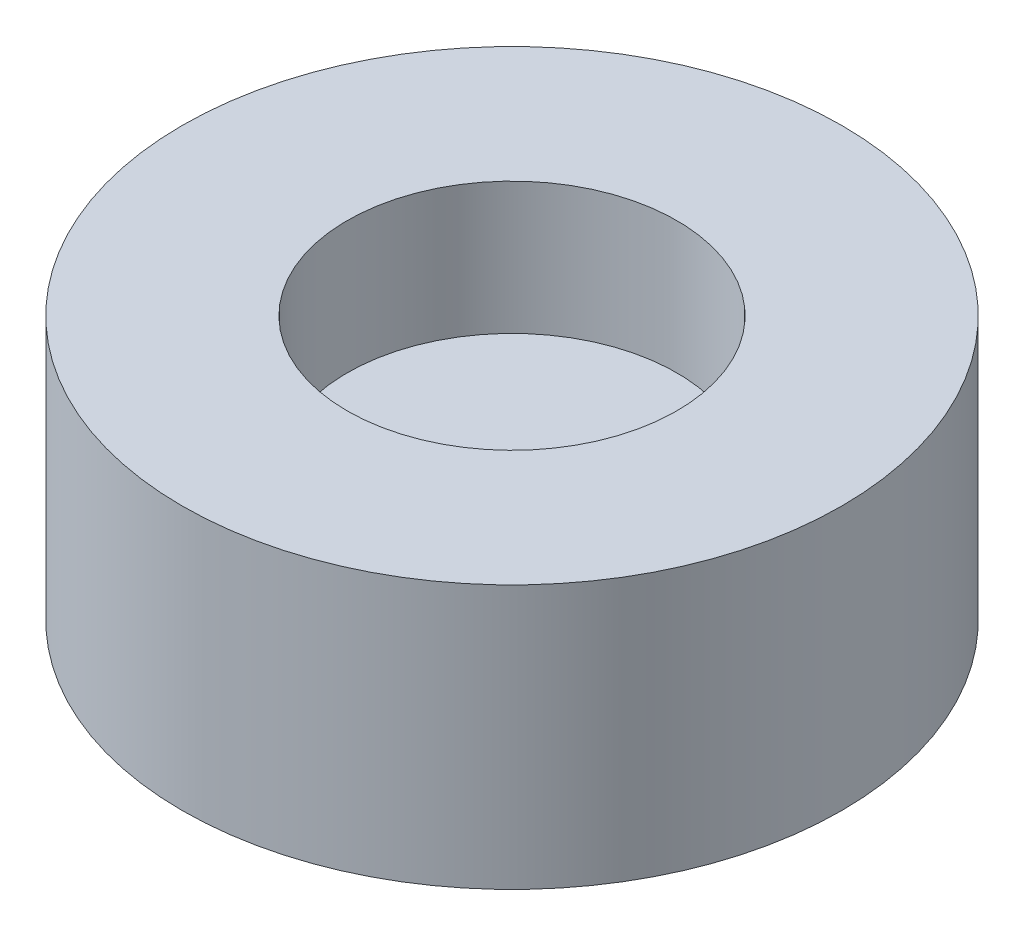
SolidWorks part; units mm, degrees
ref_plane "Front Plane" through (0, 0, 0) normal (0, 0, 1) x (1, 0, 0)
ref_plane "Top Plane" through (0, 0, 0) normal (0, 1, 0) x (1, 0, 0)
ref_plane "Right Plane" through (0, 0, 0) normal (1, 0, 0) x (0, 0, -1)
sketch "Sketch1" plane through (0, 0, 0) normal (0, 1, 0) x (1, 0, 0)
  circle A0 centre (0, 0) radius 5
  dimension "D1" = 10
extrude "Boss-Extrude1" add sketch "Sketch1" along normal blind 4
sketch "Sketch2" plane through (0, 4, 0) normal (0, 1, 0) x (1, 0, 0)
  circle A0 centre (0, 0) radius 2.5
  dimension "D1" = 5
extrude "Cut-Extrude1" cut sketch "Sketch2" against normal blind 2
